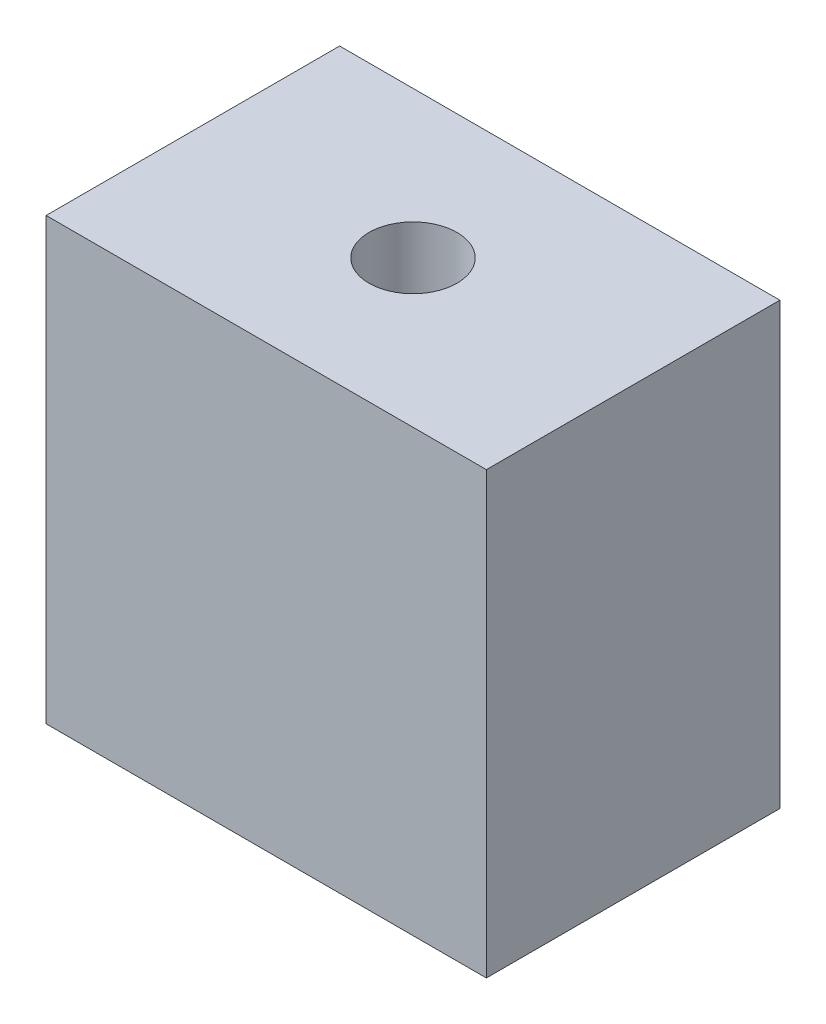
SolidWorks part; units mm, degrees
ref_plane "Front Plane" through (0, 0, 0) normal (0, 0, 1) x (1, 0, 0)
ref_plane "Top Plane" through (0, 0, 0) normal (0, 1, 0) x (1, 0, 0)
ref_plane "Right Plane" through (0, 0, 0) normal (1, 0, 0) x (0, 0, -1)
sketch "Sketch1" plane through (0, 0, 0) normal (0, 1, 0) x (1, 0, 0)
  line L1 (-38.1, 25.4) -> (0, 25.4)
  line L2 (-38.1, 25.4) -> (-38.1, 0)
  line L3 (-38.1, 0) -> (0, 0)
  line L4 (0, 25.4) -> (0, 0)
  circle A2 centre (-19.05, 12.7) radius 3.81
  point P4 (0, 0)
  dimension "D3" = 7.62
  dimension "D4" = 12.7
  dimension "D1" = 38.1
  dimension "D2" = 25.4
  dimension "D8" = 19.05
extrude "Boss-Extrude1" add sketch "Sketch1" along normal blind 38.1
